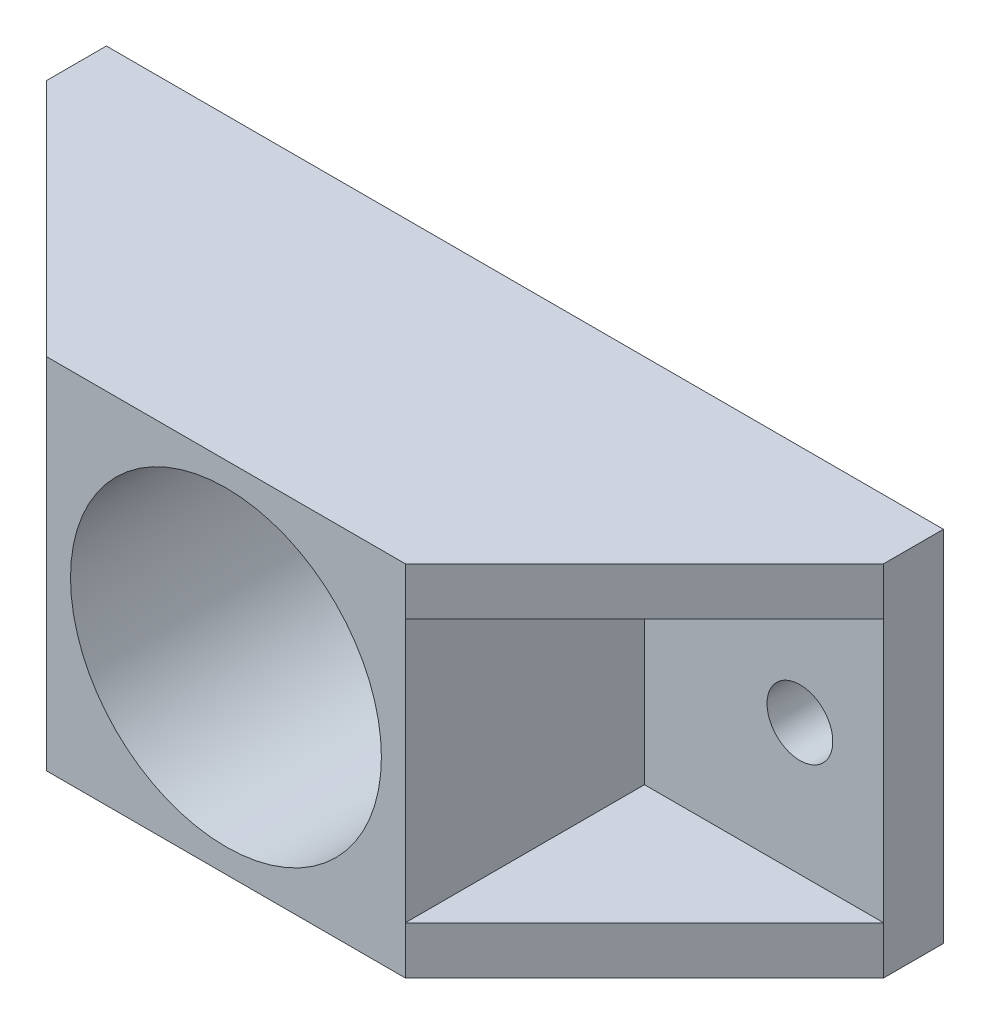
SolidWorks part; units mm, degrees
material "1.1191 (C45E)"
ref_plane "前视基准面" through (0, 0, 0) normal (0, 0, 1) x (1, 0, 0)
ref_plane "上视基准面" through (0, 0, 0) normal (0, 1, 0) x (1, 0, 0)
ref_plane "右视基准面" through (0, 0, 0) normal (1, 0, 0) x (0, 0, -1)
sketch "草图1" plane through (0, 0, 0) normal (0, 0, 1) x (1, 0, 0)
  line L0 (0, 15) -> (0, 71.2537) construction
  line L1 (-35, 15) -> (35, 15)
  line L2 (0, 0) -> (-49.1055, 0) construction
  line L3 (-35, -15) -> (35, -15)
  line L4 (-35, 15) -> (-35, -15)
  line L5 (35, 15) -> (35, -15)
  circle A1 centre (-28, 0) radius 2.75
  circle A2 centre (28, 0) radius 2.75
  point P19 (35, 15)
  point P22 (-35, 15)
  dimension "D1" = 56
  dimension "D3" = 70
  dimension "D4" = 5.5
  dimension "D2" = 30
extrude "凸台-拉伸1" add sketch "草图1" along normal blind 5
sketch "草图2" plane through (0, 0, 5) normal (0, 0, 1) x (1, 0, 0)
  line L0 (35, 15) -> (-35, 15) construction
  line L1 (15, -15) -> (-15, -15)
  line L2 (15, -15) -> (15, 15)
  line L3 (15, 15) -> (-15, 15)
  line L4 (-15, -15) -> (-15, 15)
  line L5 (15, -15) -> (-15, 15) construction
  line L6 (15, 15) -> (-15, -15) construction
  point P0 (0, 0)
  dimension "D1" = 30
extrude "凸台-拉伸2" add sketch "草图2" along normal blind 20
sketch "草图3" plane through (0, 0, 25) normal (0, 0, 1) x (1, 0, 0)
  circle A0 centre (0, 0) radius 13
extrude "切除-拉伸1" cut sketch "草图3" against normal through all
sketch "草图4" plane through (0, -15, 0) normal (0, -1, 0) x (1, 0, 0)
  line L0 (-15, 25) -> (-35, 5)
  line L1 (-35, 5) -> (-15, 5)
  line L2 (-15, 5) -> (-15, 25)
  line L3 (15, 25) -> (15, 5)
  line L4 (15, 5) -> (35, 5)
  line L5 (35, 5) -> (15, 25)
extrude "凸台-拉伸3" add sketch "草图4" against normal blind 4
mirror "镜向1" about plane through (0, 0, 0) normal (0, 1, 0) of "凸台-拉伸3"
equation "\"5。5\"=7.32439"
